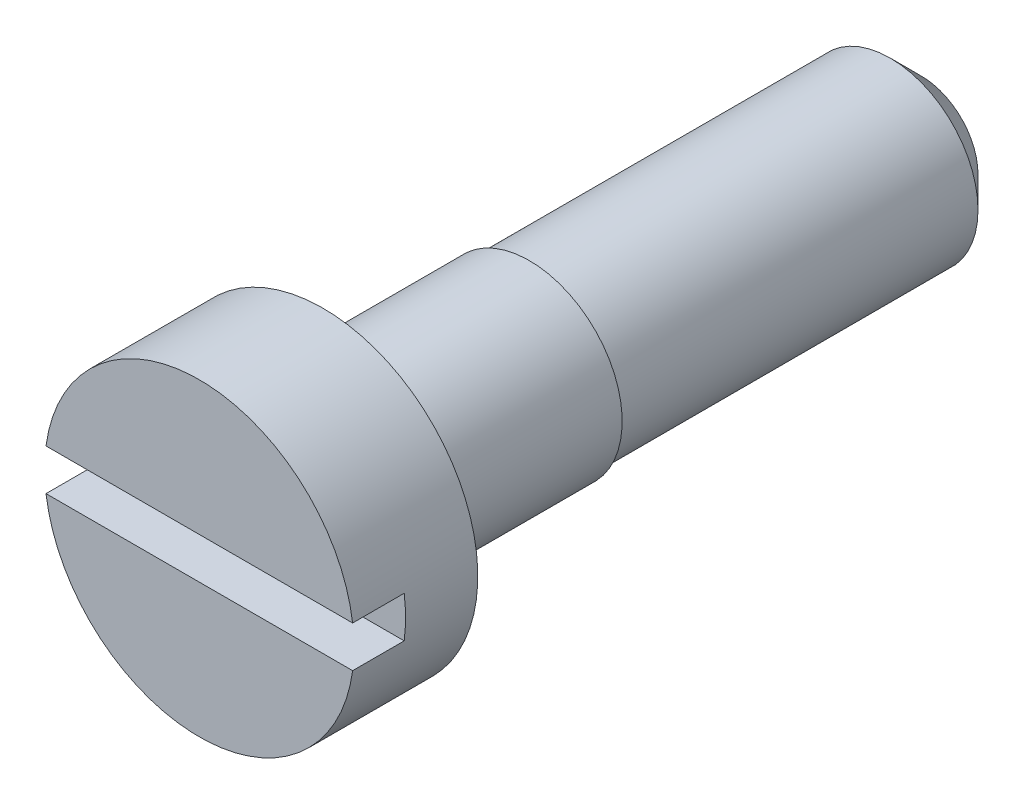
SolidWorks part; units mm, degrees
ref_plane "Front Plane" through (0, 0, 0) normal (0, 0, 1) x (1, 0, 0)
ref_plane "Top Plane" through (0, 0, 0) normal (0, 1, 0) x (1, 0, 0)
ref_plane "Right Plane" through (0, 0, 0) normal (1, 0, 0) x (0, 0, -1)
sketch "Sketch2" plane through (0, 0, 0) normal (0, 0, 1) x (1, 0, 0)
  circle A0 centre (0, 0) radius 1.5
  dimension "D1" = 3
extrude "Boss-Extrude1" add sketch "Sketch2" against normal blind 7 contours A0
sketch "Sketch4" plane through (0, 0, -7) normal (0, 0, -1) x (-1, 0, 0)
  circle A0 centre (0, 0) radius 0.9
  dimension "D1" = 1.8
extrude "Cut-Extrude1" cut sketch "Sketch4" against normal blind 5.8 flip side to cut
sketch "Sketch5" plane through (0, 0, -7) normal (0, 0, -1) x (-1, 0, 0)
  circle A0 centre (0, 0) radius 0.85
  dimension "D1" = 1.7
extrude "Cut-Extrude2" cut sketch "Sketch5" against normal blind 3.8 flip side to cut
cosmetic thread "Cosmetic Thread1" parameters "D1"=3.3, "D2"=1.3
sketch "Sketch6" plane through (0, 0, 0) normal (0, 0, 1) x (1, 0, 0)
  line L1 (-1.6, -0.2) -> (1.6, -0.2)
  line L2 (-1.6, -0.2) -> (-1.6, 0.2)
  line L3 (-1.6, 0.2) -> (1.6, 0.2)
  line L4 (1.6, -0.2) -> (1.6, 0.2)
  line L5 (-1.6, -0.2) -> (1.6, 0.2) construction
  line L6 (-1.6, 0.2) -> (1.6, -0.2) construction
  circle A3 centre (0, 0) radius 1.5 construction
  point P0 (0, 0)
  dimension "D1" = 0.4
  dimension "D2" = 0.1
extrude "Cut-Extrude3" cut sketch "Sketch6" against normal blind 0.5 contours L3 L4 L1 L2
chamfer "Chamfer1" distance 0.3 angle 45 1 edges at (-0.85, 0, -7)
